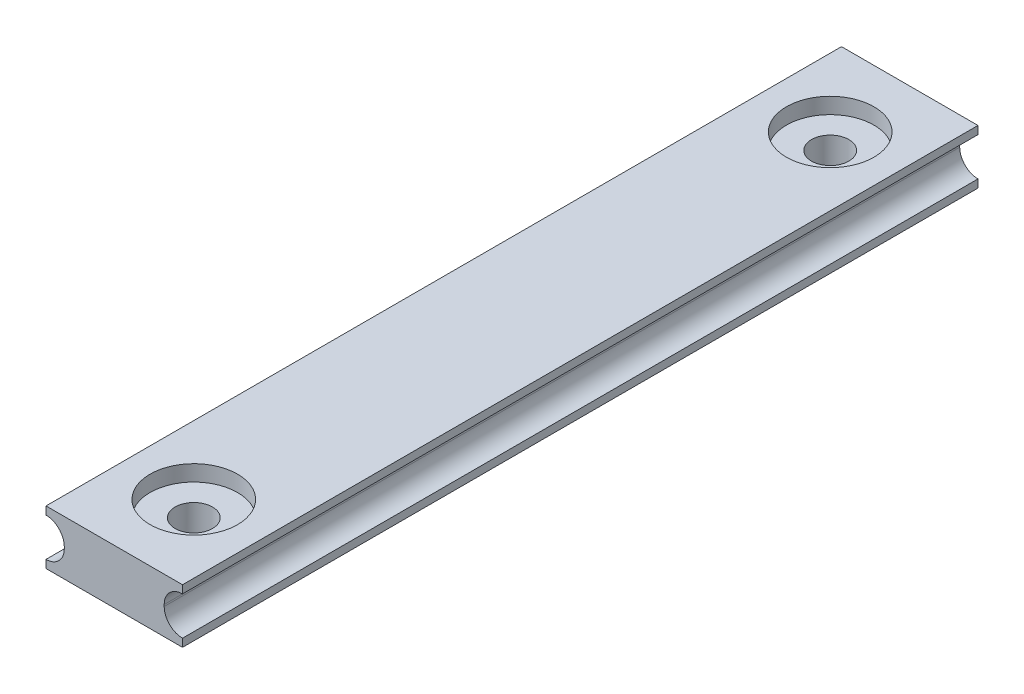
SolidWorks part; units mm, degrees
ref_plane "Front Plane" through (0, 0, 0) normal (0, 0, 1) x (1, 0, 0)
ref_plane "Top Plane" through (0, 0, 0) normal (0, 1, 0) x (1, 0, 0)
ref_plane "Right Plane" through (0, 0, 0) normal (1, 0, 0) x (0, 0, -1)
sketch "Sketch1" plane through (0, 0, 0) normal (0, 0, 1) x (1, 0, 0)
  line L0 (0, 0) -> (0, 2.8653) construction
  line L1 (0, 0) -> (3.9378, 0) construction
  line L2 (-3.14, 0.055) -> (-3.14, -0.055)
  line L3 (-4.29, 1.705) -> (4.29, 1.705)
  line L4 (-4.29, 1.705) -> (-4.29, 1.205)
  line L5 (-4.29, -1.705) -> (4.29, -1.705)
  line L6 (4.29, 1.705) -> (4.29, 1.205)
  line L7 (3.14, 0.055) -> (3.14, -0.055)
  line L8 (4.29, -1.205) -> (4.29, -1.705)
  line L9 (-4.29, -1.205) -> (-4.29, -1.705)
  arc A0 (3.14, 0.055) -> (4.29, 1.205) centre (4.29, 0.055) cw
  arc A1 (3.14, -0.055) -> (4.29, -1.205) centre (4.29, -0.055) ccw
  arc A2 (-3.14, 0.055) -> (-4.29, 1.205) centre (-4.29, 0.055) ccw
  arc A3 (-3.14, -0.055) -> (-4.29, -1.205) centre (-4.29, -0.055) cw
  dimension "D5" = 1.15
  dimension "D1" = 8.58
  dimension "D2" = 3.41
  dimension "D3" = 0.11
  dimension "D4" = 6.28
extrude "Boss-Extrude1" add sketch "Sketch1" along normal mid plane 50
sketch "Sketch2" plane through (0, 1.705, 0) normal (0, 1, 0) x (1, 0, 0)
  line L1 (0, 0) -> (0, 6.7591) construction
  line L2 (4.29, 25) -> (-4.29, 25) construction
  circle A0 centre (0, 20) radius 1.175
  dimension "D1" = 2.35
  dimension "D2" = 5
extrude "Cut-Extrude1" cut sketch "Sketch2" against normal through all
sketch "Sketch3" plane through (0, 1.705, 0) normal (0, 1, 0) x (1, 0, 0)
  circle A0 centre (0, 20) radius 2.75
  dimension "D1" = 5.5
extrude "Cut-Extrude2" cut sketch "Sketch3" against normal blind 1
mirror "Mirror1" about plane through (0, 0, 0) normal (0, 0, 1) of "Cut-Extrude2", "Cut-Extrude1"
